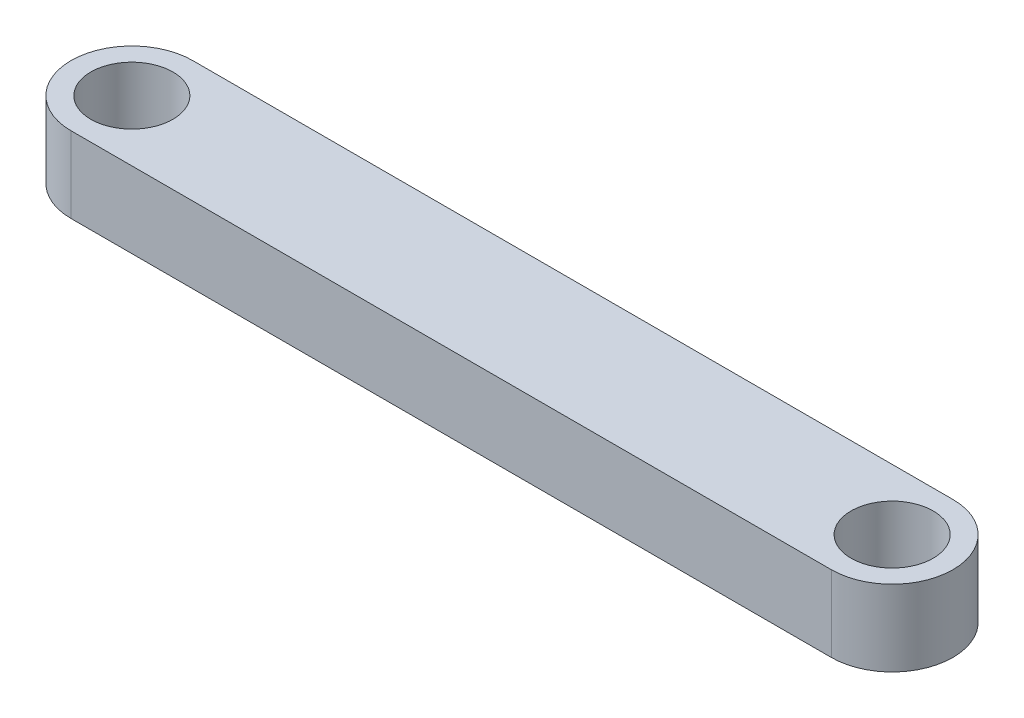
SolidWorks part; units mm, degrees
ref_plane "Front Plane" through (0, 0, 0) normal (0, 0, 1) x (1, 0, 0)
ref_plane "Top Plane" through (0, 0, 0) normal (0, 1, 0) x (1, 0, 0)
ref_plane "Right Plane" through (0, 0, 0) normal (1, 0, 0) x (0, 0, -1)
sketch "Sketch1" plane through (0, 0, 0) normal (0, 1, 0) x (1, 0, 0)
  line L0 (-25, 0) -> (25, 0) construction
  line L1 (-25, 4) -> (25, 4)
  line L2 (-25, -4) -> (25, -4)
  arc A0 (-25, 4) -> (-25, -4) centre (-25, 0) ccw
  arc A1 (25, -4) -> (25, 4) centre (25, 0) ccw
  circle A2 centre (-25, 0) radius 2.7
  circle A3 centre (25, 0) radius 2.7
  point P3 (0, 0)
  dimension "D2" = 4
  dimension "D3" = 5.4
  dimension "D4" = 5.4
  dimension "D1" = 50
extrude "Boss-Extrude1" add sketch "Sketch1" along normal blind 5
equation "\"D4@Sketch1\"=\"D3@Sketch1\""
